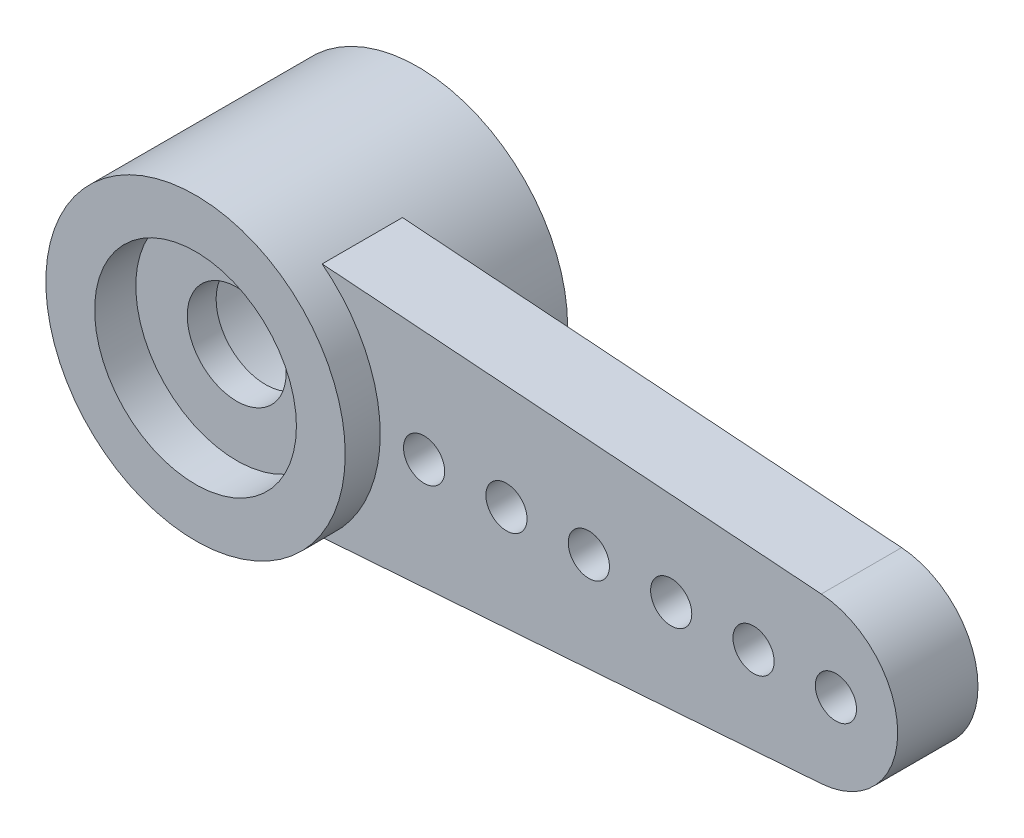
SolidWorks part; units mm, degrees
ref_plane "Plan de face" through (0, 0, 0) normal (0, 0, 1) x (1, 0, 0)
ref_plane "Plan de dessus" through (0, 0, 0) normal (0, 1, 0) x (1, 0, 0)
ref_plane "Plan de droite" through (0, 0, 0) normal (1, 0, 0) x (0, 0, -1)
sketch "Esquisse1" plane through (0, 0, 0) normal (0, 0, 1) x (1, 0, 0)
  circle A0 centre (0, 0) radius 1.2
  circle A1 centre (0, 0) radius 3.635
  dimension "D1" = 2.4
  dimension "D2" = 7.27
extrude "Boss.-Extru.1" add sketch "Esquisse1" along normal blind 5.4
ref_plane "Plan1" through (0, 0, 4.55) normal (0, 0, 1) x (1, 0, 0)
sketch "Esquisse2" plane through (0, 0, 4.55) normal (0, 0, 1) x (1, 0, 0)
  line L0 (0, 0) -> (17.4633, 0) construction
  line L1 (2.2243, 2.875) -> (14.3449, 1.9947)
  line L2 (2.2243, -2.875) -> (14.3449, -1.9947)
  arc A1 (14.3449, -1.9947) -> (14.3449, 1.9947) centre (14.2, 0) ccw
  circle A2 centre (0, 0) radius 3.635 construction
  arc A3 (2.2243, 2.875) -> (2.2243, -2.875) centre (0, 0) cw
  dimension "D2" = 2
  dimension "D3" = 2.875
extrude "Boss.-Extru.2" add sketch "Esquisse2" against normal blind 1.95 contours A3 L0 A1 L1 | L0 A3 L2 A1
sketch "Esquisse3" plane through (0, 0, 5.4) normal (0, 0, 1) x (1, 0, 0)
  circle A0 centre (0, 0) radius 2.45
extrude "Enlèv. mat.-Extru.1" cut sketch "Esquisse3" against normal blind 1
sketch "Esquisse4" plane through (0, 0, 0) normal (0, 0, -1) x (-1, 0, 0)
  circle A0 centre (0, 0) radius 2.45
  dimension "D1" = 4.9
extrude "Enlèv. mat.-Extru.2" cut sketch "Esquisse4" against normal blind 3.7
sketch "Esquisse5" plane through (0, 0, 4.55) normal (0, 0, 1) x (1, 0, 0)
  line L0 (3.635, 0) -> (16.2, 0) construction
  line L1 (11.7, 0.6093) -> (11.7, -0.6406) construction
  arc A0 (2.2243, -2.875) -> (2.2243, 2.875) centre (0, 0) ccw construction
  arc A1 (14.3449, -1.9947) -> (14.3449, 1.9947) centre (14.2, 0) ccw construction
  circle A2 centre (14.7, 0) radius 0.5
  circle A3 centre (12.7, 0) radius 0.5
  circle A4 centre (10.7, 0) radius 0.5
  circle A5 centre (8.7, 0) radius 0.5
  circle A6 centre (6.7, 0) radius 0.5
  circle A7 centre (4.7, 0) radius 0.5
  dimension "D2" = 1
  dimension "D1" = 1.5
  dimension "D3" = 3
  dimension "D4" = 6
extrude "Enlèv. mat.-Extru.3" cut sketch "Esquisse5" against normal blind 3.7
